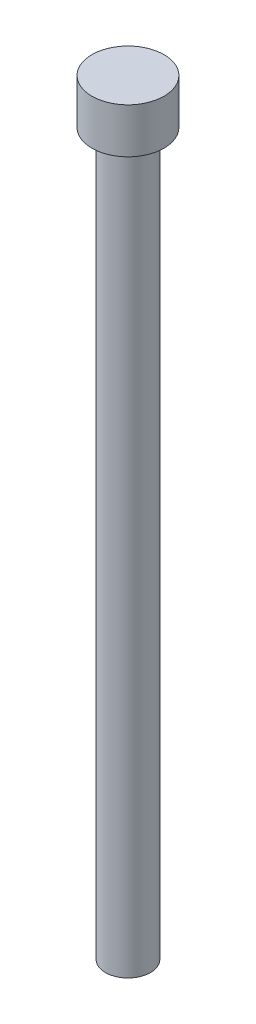
SolidWorks part; units mm, degrees
ref_plane "Front Plane" through (0, 0, 0) normal (0, 0, 1) x (1, 0, 0)
ref_plane "Top Plane" through (0, 0, 0) normal (0, 1, 0) x (1, 0, 0)
ref_plane "Right Plane" through (0, 0, 0) normal (1, 0, 0) x (0, 0, -1)
sketch "Sketch1" plane through (0, 0, 0) normal (0, 1, 0) x (1, 0, 0)
  circle A0 centre (0, 0) radius 3.175
  dimension "D1" = 6.35
extrude "Boss-Extrude1" add sketch "Sketch1" along normal blind 101.6
sketch "Sketch2" plane through (0, 101.6, 0) normal (0, 1, 0) x (1, 0, 0)
  circle A0 centre (0, 0) radius 5.08
  dimension "D1" = 10.16
extrude "Boss-Extrude2" add sketch "Sketch2" along normal blind 6.35
